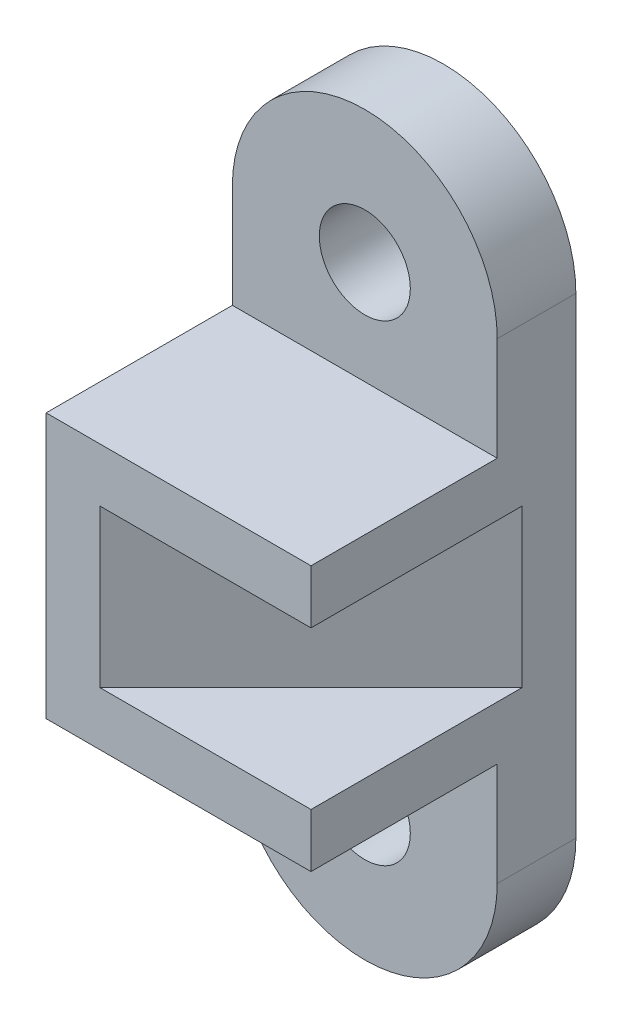
SolidWorks part; units mm, degrees
ref_plane "Front Plane" through (0, 0, 0) normal (1, 0, 0) x (0, 1, 0)
ref_plane "Top Plane" through (0, 0, 0) normal (0, 0, 1) x (0, 1, 0)
ref_plane "Right Plane" through (0, 0, 0) normal (0, 1, 0) x (-1, 0, 0)
sketch "Sketch1" plane through (0, 0, 0) normal (0, 0, 1) x (0, 1, 0)
  line L0 (0, 64) -> (0, 0) construction
  line L1 (0, 0) -> (114, 0)
  line L3 (0, 64) -> (114, 64)
  line L5 (114, 64) -> (114, 0) construction
  arc A0 (0, 64) -> (0, 0) centre (0, 32) ccw
  arc A1 (114, 0) -> (114, 64) centre (114, 32) ccw
  circle A2 centre (0, 32) radius 11
  circle A3 centre (114, 32) radius 11
  dimension "D3" = 32
  dimension "D4" = 32
  dimension "D5" = 22
  dimension "D6" = 22
  dimension "D1" = 114
  dimension "D2" = 64
extrude "Boss-Extrude1" add sketch "Sketch1" along normal blind 19
sketch "Sketch2" plane through (0, 0, 19) normal (0, 0, 1) x (1, 0, 0)
  line L0 (0, 57) -> (0, 89)
  line L1 (0, 0) -> (0, 114) construction
  line L2 (0, 89) -> (-64, 89)
  line L3 (-64, 114) -> (-64, 0) construction
  line L4 (-64, 89) -> (-64, 25)
  line L5 (-64, 25) -> (0, 25)
  line L6 (0, 25) -> (0, 57)
  dimension "D1" = 32
  dimension "D2" = 32
extrude "Boss-Extrude2" add sketch "Sketch2" along normal blind 45
sketch "Sketch3" plane through (0, 0, 64) normal (0, 0, 1) x (1, 0, 0)
  line L4 (-13, 76) -> (0, 76)
  line L5 (0, 25) -> (0, 89) construction
  line L6 (0, 76) -> (0, 38)
  line L7 (0, 38) -> (-13, 38)
  line L8 (-13, 38) -> (-13, 76)
  line L9 (-13, 76) -> (-51, 76)
  line L10 (-51, 76) -> (-51, 38)
  line L11 (-51, 38) -> (-13, 38)
  line L13 (-13, 76) -> (-51, 76)
  line L14 (-51, 76) -> (-51, 38)
  line L15 (-51, 38) -> (-13, 38)
  dimension "D1" = 13
extrude "Cut-Extrude1" cut sketch "Sketch3" against normal blind 51
sketch "Sketch4" plane through (0, 38, 0) normal (0, 1, 0) x (1, 0, 0)
  line L0 (0, -13) -> (-51, -64)
  line L1 (-51, -64) -> (-51, -13)
  line L2 (-51, -13) -> (0, -13)
extrude "Boss-Extrude3" add sketch "Sketch4" along normal up to next
